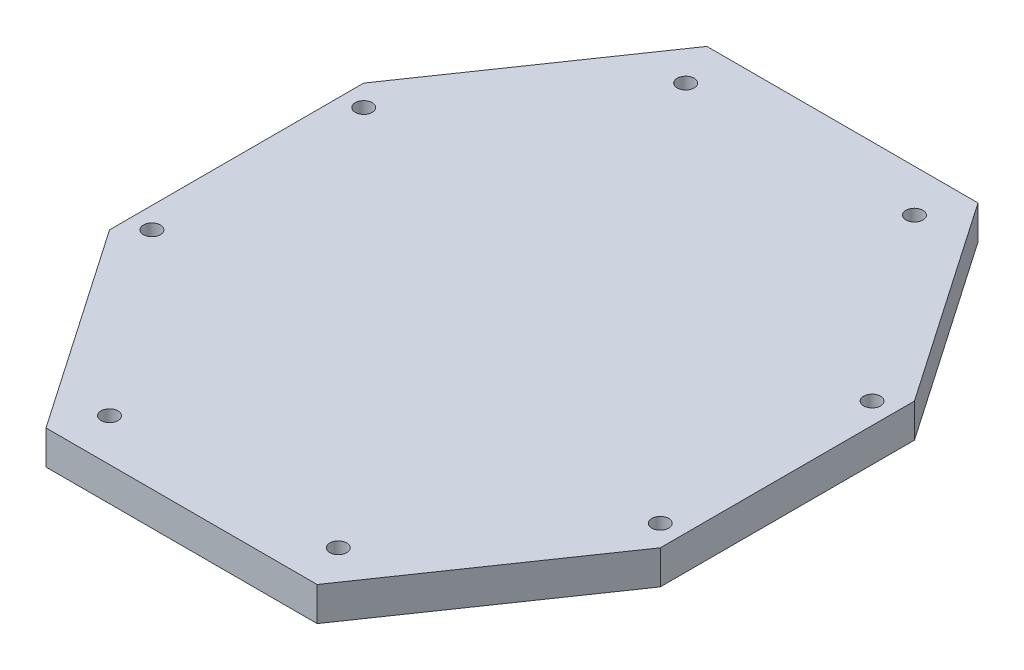
SolidWorks part; units mm, degrees
ref_plane "Front" through (0, 0, 0) normal (0, 0, 1) x (1, 0, 0)
ref_plane "Top" through (0, 0, 0) normal (0, 1, 0) x (1, 0, 0)
ref_plane "Right" through (0, 0, 0) normal (1, 0, 0) x (0, 0, -1)
sketch "草图1" plane through (0, 0, 0) normal (0, 1, 0) x (1, 0, 0)
  line L0 (0, 0) -> (60, 0) construction
  line L1 (60, 0) -> (60, -50) construction
  line L2 (60, 0) -> (60, 43) construction
  line L3 (0, 0) -> (0, 43) construction
  line L4 (0, 43) -> (27, 43) construction
  line L5 (0, -93) -> (27, -93) construction
  line L6 (60, -25) -> (70, -25) construction
  line L7 (0, -50) -> (0, -93) construction
  line L8 (60, -50) -> (0, -50) construction
  line L9 (70, -25) -> (70, 53) construction
  line L10 (0, 53) -> (32, 53) construction
  line L11 (65, -25) -> (65, 5) construction
  line L12 (32, 53) -> (65, 5)
  line L13 (65, 5) -> (65, -55)
  line L14 (-32, 53) -> (32, 53)
  line L15 (32, -103) -> (65, -55)
  line L16 (-32, -103) -> (32, -103)
  line L17 (-32, -103) -> (-65, -55)
  line L18 (-65, 5) -> (-65, -55)
  line L19 (-32, 53) -> (-65, 5)
  circle A0 centre (27, -93) radius 2
  circle A1 centre (27, 43) radius 2
  circle A2 centre (60, 0) radius 2
  circle A3 centre (60, -50) radius 2
  circle A4 centre (-27, -93) radius 2
  circle A5 centre (-60, -50) radius 2
  circle A6 centre (-60, 0) radius 2
  circle A7 centre (-27, 43) radius 2
  point P4 (0, 0)
  point P8 (0, 0)
  point P11 (60, 0)
  point P12 (0, 43)
  point P38 (0, -103)
extrude "凸台-拉伸1" add sketch "草图1" along normal blind 8
